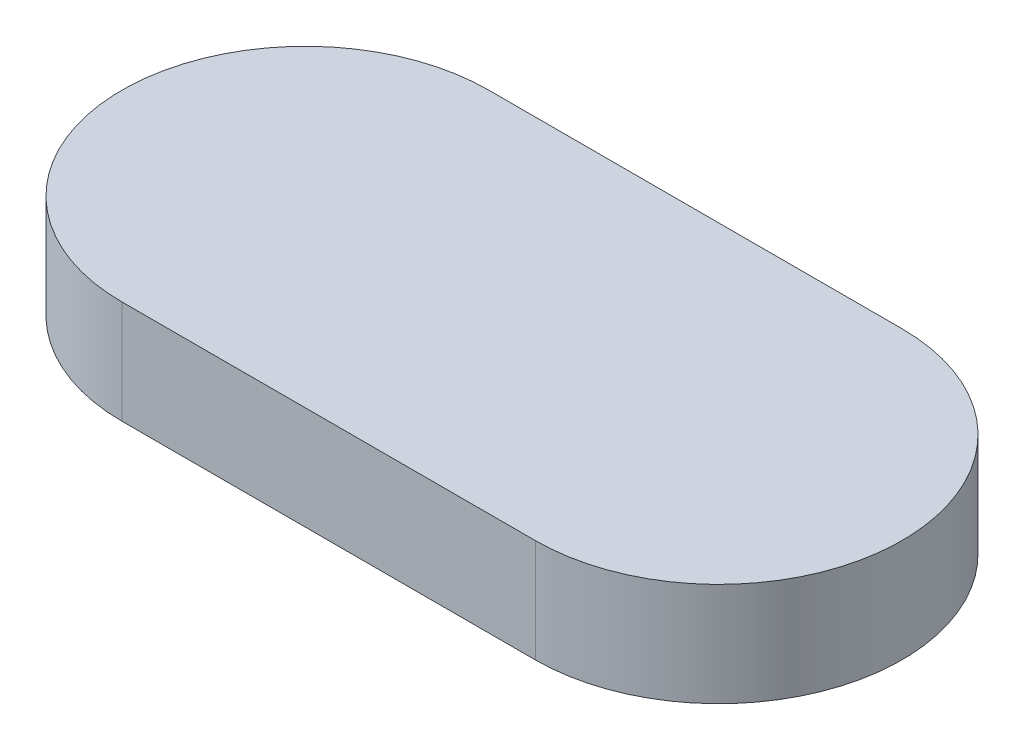
SolidWorks part; units mm, degrees
ref_plane "Ebene vorne" through (0, 0, 0) normal (0, 0, 1) x (1, 0, 0)
ref_plane "Ebene oben" through (0, 0, 0) normal (0, 1, 0) x (1, 0, 0)
ref_plane "Ebene rechts" through (0, 0, 0) normal (1, 0, 0) x (0, 0, -1)
sketch "Skizze1" plane through (0, 0, 0) normal (0, 1, 0) x (1, 0, 0)
  line L0 (-10, 0) -> (10, 0) construction
  line L1 (-10, 8.875) -> (10, 8.875)
  line L2 (-10, -8.875) -> (10, -8.875)
  arc A0 (-10, 8.875) -> (-10, -8.875) centre (-10, 0) ccw
  arc A1 (10, -8.875) -> (10, 8.875) centre (10, 0) ccw
  point P3 (0, 0)
  point P8 (0, 0)
extrude "Aufsatz-Linear austragen1" add sketch "Skizze1" along normal blind 5
